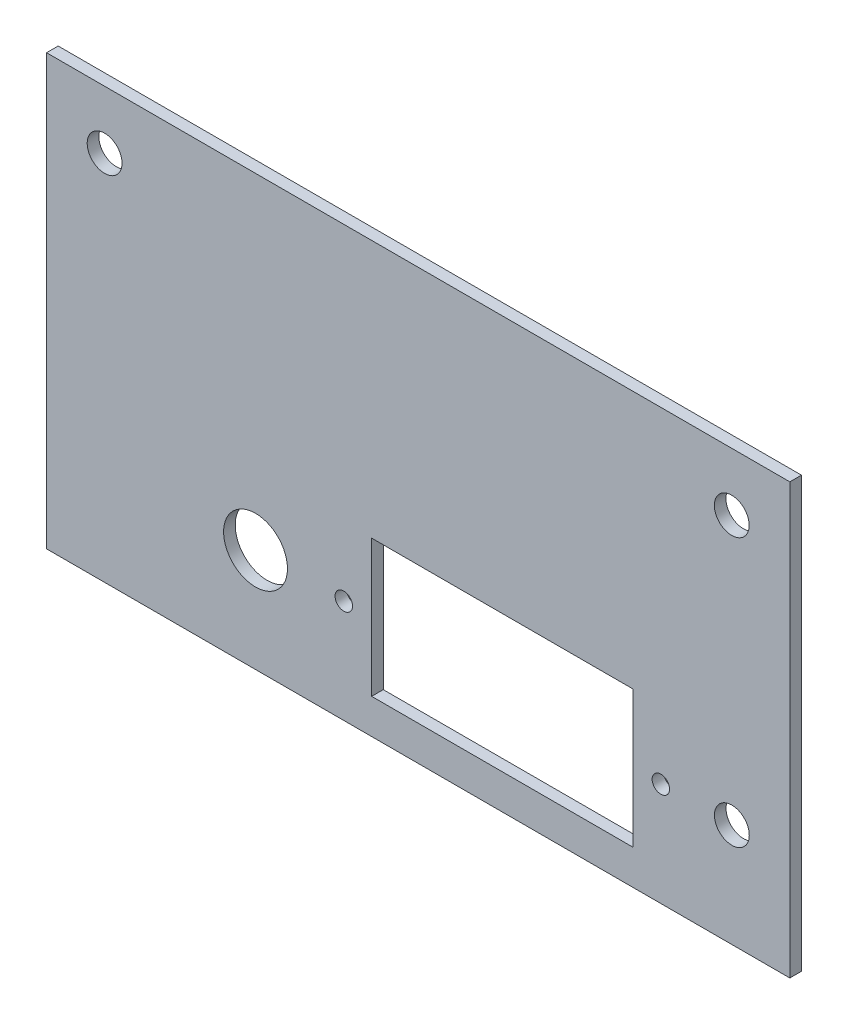
SolidWorks part; units mm, degrees
ref_plane "Alzado" through (0, 0, 0) normal (0, 0, 1) x (1, 0, 0)
ref_plane "Planta" through (0, 0, 0) normal (0, 1, 0) x (1, 0, 0)
ref_plane "Vista lateral" through (0, 0, 0) normal (1, 0, 0) x (0, 0, -1)
sketch "Croquis1" plane through (0, 0, 0) normal (0, 0, 1) x (1, 0, 0)
  line L1 (-23.3171, 25.5049) -> (40.6829, 25.5049)
  line L2 (-23.3171, 25.5049) -> (-23.3171, -11.4951)
  line L3 (-23.3171, -11.4951) -> (40.6829, -11.4951)
  line L4 (40.6829, 25.5049) -> (40.6829, -11.4951)
  line L5 (4.6761, 3.3049) -> (27.1761, 3.3049)
  line L6 (4.6761, 3.3049) -> (4.6761, -8.4951)
  line L7 (4.6761, -8.4951) -> (27.1761, -8.4951)
  line L8 (27.1761, 3.3049) -> (27.1761, -8.4951)
  line L9 (8.6829, 25.5049) -> (8.6829, -11.4951) construction
  line L10 (-5.3239, -2.5951) -> (21.2093, -2.5951) construction
  circle A0 centre (-18.3171, 20.5049) radius 1.5
  circle A6 centre (35.6829, 20.5049) radius 1.5
  circle A7 centre (29.5761, -2.5951) radius 0.75
  circle A8 centre (2.2761, -2.5951) radius 0.75
  circle A9 centre (-5.3239, -2.5951) radius 2.75
  circle A10 centre (35.6907, -2.5951) radius 1.5
  circle A12 centre (21.2093, -2.5951) radius 1.5 construction
  circle A15 centre (-9.3171, 20.5049) radius 1.5 [skipped]
  circle A16 centre (-0.3171, 20.5049) radius 1.5 [skipped]
  circle A17 centre (8.6829, 20.5049) radius 1.5 [skipped]
  circle A18 centre (17.6829, 20.5049) radius 1.5 [skipped]
  circle A19 centre (26.6829, 20.5049) radius 1.5 [skipped]
  dimension "D1" = 7
  dimension "D2" = 64
  dimension "D4" = 37
  dimension "D8" = 2.4
  dimension "D9" = 2.4
  dimension "D11" = 3
  dimension "D10" = 5.9
  dimension "D12" = 5.9
  dimension "D13" = 5.9
  dimension "D14" = 5.9
  dimension "D15" = 4.0068
  dimension "D16" = 10
  dimension "D17" = 8.5146
  dimension "D3" = 5
  dimension "D5" = 5
  dimension "D6" = 22.5
  dimension "D7" = 11.8
extrude "Saliente-Extruir1" add sketch "Croquis1" along normal blind 1
